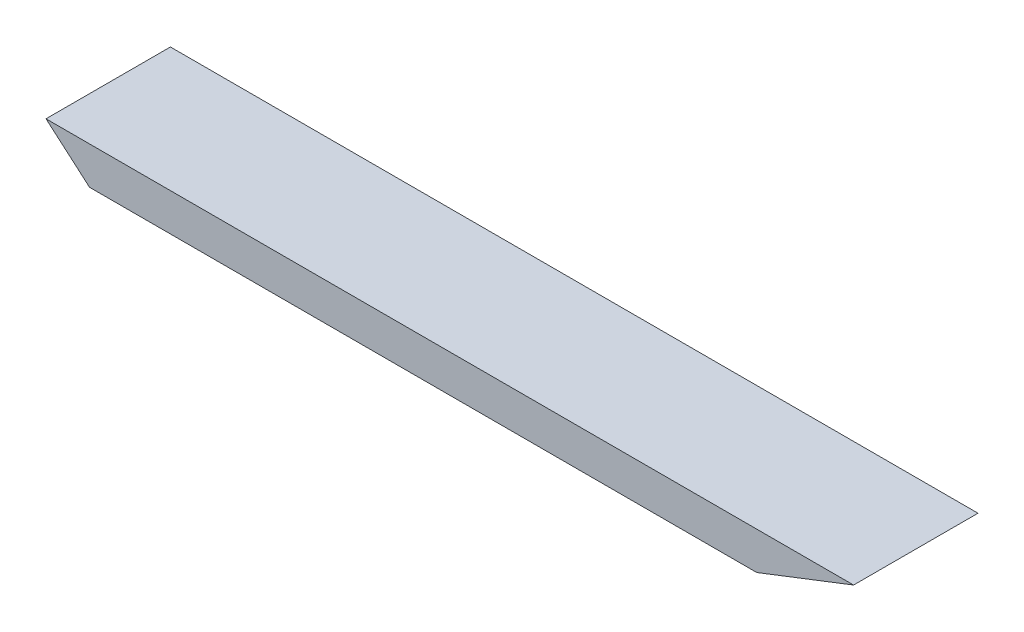
SolidWorks part; units mm, degrees
ref_plane "Plan de face" through (0, 0, 0) normal (0, 0, 1) x (1, 0, 0)
ref_plane "Plan de dessus" through (0, 0, 0) normal (0, 1, 0) x (1, 0, 0)
ref_plane "Plan de droite" through (0, 0, 0) normal (1, 0, 0) x (0, 0, -1)
sketch "Esquisse1" plane through (0, 0, 0) normal (0, 0, 1) x (1, 0, 0)
  line L0 (-14.3522, 3.6445) -> (24.5978, 3.6445)
  line L1 (24.5978, 3.6445) -> (19.9281, 1.8323)
  line L2 (19.9281, 1.8323) -> (-12.2519, 1.8323)
  line L3 (-12.2519, 1.8323) -> (-14.3522, 3.6445)
  dimension "D1" = 38.95
  dimension "D2" = 40.79
  dimension "D3" = 32.18
  dimension "D4" = 21.21
extrude "Boss.-Extru.1" add sketch "Esquisse1" along normal blind 6
